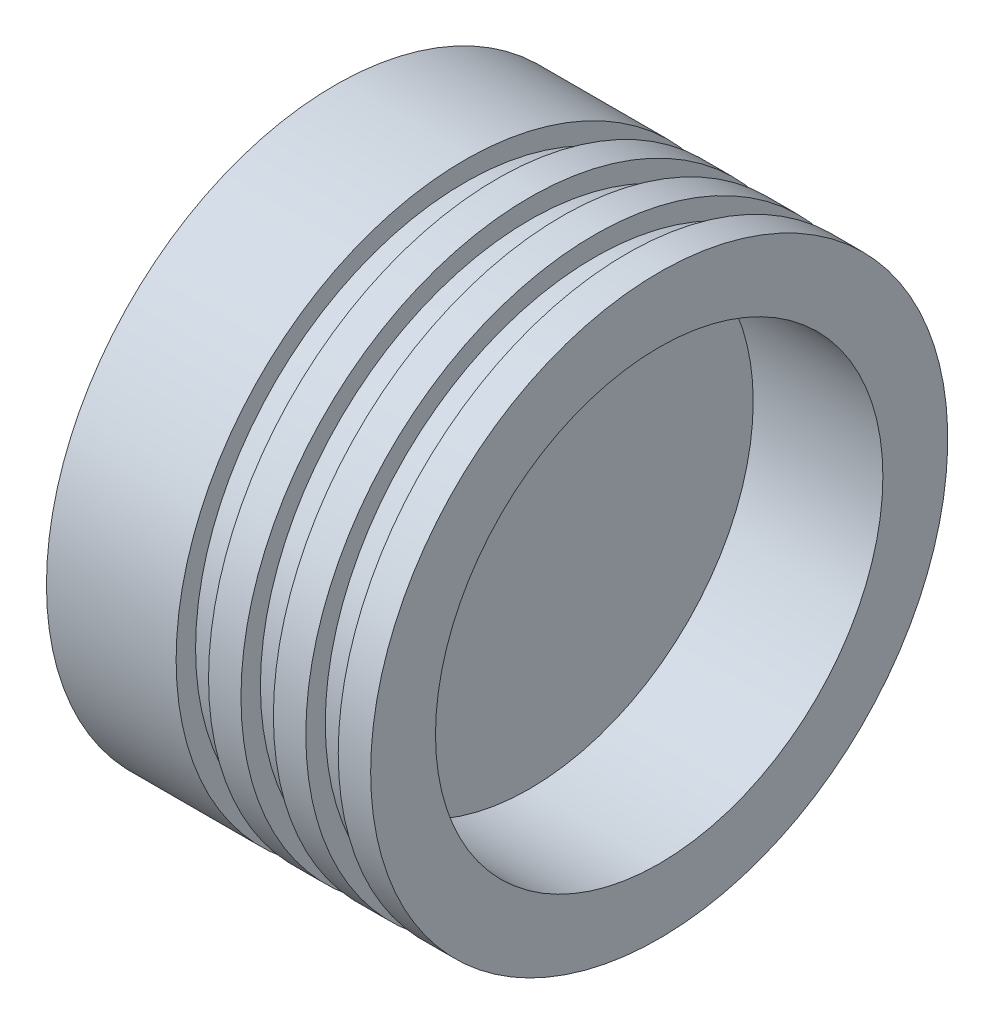
SolidWorks part; units mm, degrees
material "6063-T6"
ref_plane "Front Plane" through (0, 0, 0) normal (0, 0, 1) x (1, 0, 0)
ref_plane "Top Plane" through (0, 0, 0) normal (0, 1, 0) x (1, 0, 0)
ref_plane "Right Plane" through (0, 0, 0) normal (1, 0, 0) x (0, 0, -1)
sketch "Sketch1" plane through (0, 0, 0) normal (0, 0, 1) x (1, 0, 0)
  line L0 (0, 0) -> (30, 0) construction
  line L1 (0, 0) -> (0, 44.5)
  line L2 (0, 44.5) -> (20, 44.5)
  line L3 (20, 44.5) -> (20, 41.5)
  line L4 (20, 41.5) -> (25, 41.5)
  line L5 (25, 41.5) -> (25, 44.5)
  line L6 (25, 44.5) -> (30, 44.5)
  line L7 (30, 44.5) -> (30, 41.5)
  line L8 (30, 41.5) -> (35, 41.5)
  line L9 (35, 41.5) -> (35, 44.5)
  line L10 (35, 44.5) -> (40, 44.5)
  line L11 (40, 44.5) -> (40, 41.5)
  line L12 (40, 41.5) -> (45, 41.5)
  line L13 (45, 41.5) -> (45, 44.5)
  line L14 (45, 44.5) -> (50, 44.5)
  line L15 (50, 44.5) -> (50, 34.5)
  line L16 (50, 34.5) -> (30, 34.5)
  line L17 (30, 34.5) -> (30, 0)
  line L18 (30, 0) -> (0, 0)
  dimension "D1" = 50
  dimension "D2" = 44.5
  dimension "D3" = 5
  dimension "D4" = 5
  dimension "D5" = 5
  dimension "D6" = 3
  dimension "D7" = 10
  dimension "D8" = 20
revolve "Revolve1" add sketch "Sketch1" angle 360 about L0
